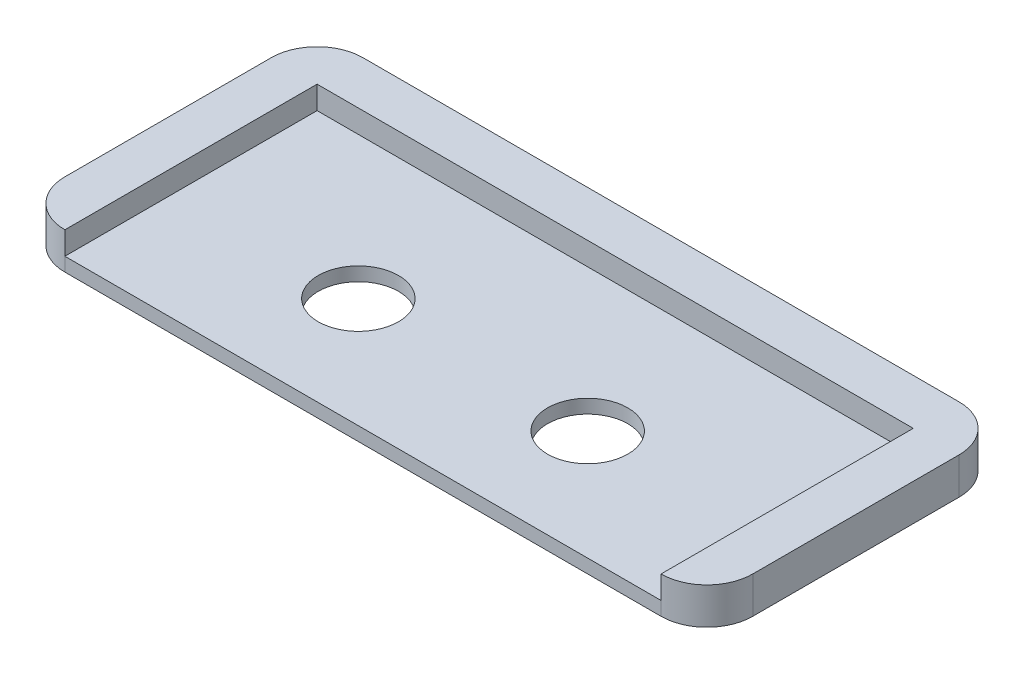
SolidWorks part; units mm, degrees
ref_plane "Front Plane" through (0, 0, 0) normal (0, 0, 1) x (1, 0, 0)
ref_plane "Top Plane" through (0, 0, 0) normal (0, 1, 0) x (1, 0, 0)
ref_plane "Right Plane" through (0, 0, 0) normal (1, 0, 0) x (0, 0, -1)
sketch "Sketch1" plane through (0, 0, 0) normal (0, 1, 0) x (1, 0, 0)
  line L1 (-15, 6.5) -> (15, 6.5)
  line L2 (-15, 6.5) -> (-15, -6.5)
  line L3 (-15, -6.5) -> (15, -6.5)
  line L4 (15, 6.5) -> (15, -6.5)
  line L5 (-15, 6.5) -> (15, -6.5) construction
  line L6 (-15, -6.5) -> (15, 6.5) construction
  point P0 (0, 0)
  dimension "D1" = 30
  dimension "D2" = 13
extrude "Boss-Extrude1" add sketch "Sketch1" along normal blind 0.6
sketch "Sketch2" plane through (0, 0.6, 0) normal (0, 1, 0) x (1, 0, 0)
  line L0 (-13, 4.5) -> (13, 4.5)
  line L1 (-15, 6.5) -> (15, 6.5)
  line L2 (-15, 6.5) -> (-15, -6.5)
  line L4 (15, 6.5) -> (15, -6.5)
  line L8 (-15, -6.5) -> (15, -6.5) construction
  line L9 (-13, -4.5) -> (13, -4.5) construction
  line L10 (-13, 4.5) -> (-13, -4.5) construction
  line L11 (13, 4.5) -> (13, -4.5) construction
  line L12 (-13, 4.5) -> (-13, -6.5)
  line L13 (-15, -6.5) -> (15, -6.5) construction
  line L14 (-13, -6.5) -> (-15, -6.5)
  line L15 (13, 4.5) -> (13, -6.5)
  line L16 (13, -6.5) -> (15, -6.5)
  dimension "D1" = 2
extrude "Boss-Extrude2" add sketch "Sketch2" along normal blind 1
fillet "Fillet1" radius 2 4 edges at (-15, 0.8, 6.5) (15, 0.8, 6.5) (15, 0.8, -6.5) (-15, 0.8, -6.5)
sketch "Sketch3" plane through (0, 0, 0) normal (0, -1, 0) x (1, 0, 0)
  line L0 (-13, 6.5) -> (13, 6.5) construction
  line L1 (0, 6.5) -> (0, -6.5) construction
  line L2 (13, -6.5) -> (-13, -6.5) construction
  circle A0 centre (-5, 1.7) radius 1.75
  circle A1 centre (5, 1.7) radius 1.75
  dimension "D3" = 3.5
  dimension "D4" = 3.5
  dimension "D6" = 5
  dimension "D1" = 8.2
  dimension "D2" = 8.2
  dimension "D5" = 5
extrude "Cut-Extrude1" cut sketch "Sketch3" against normal through all
